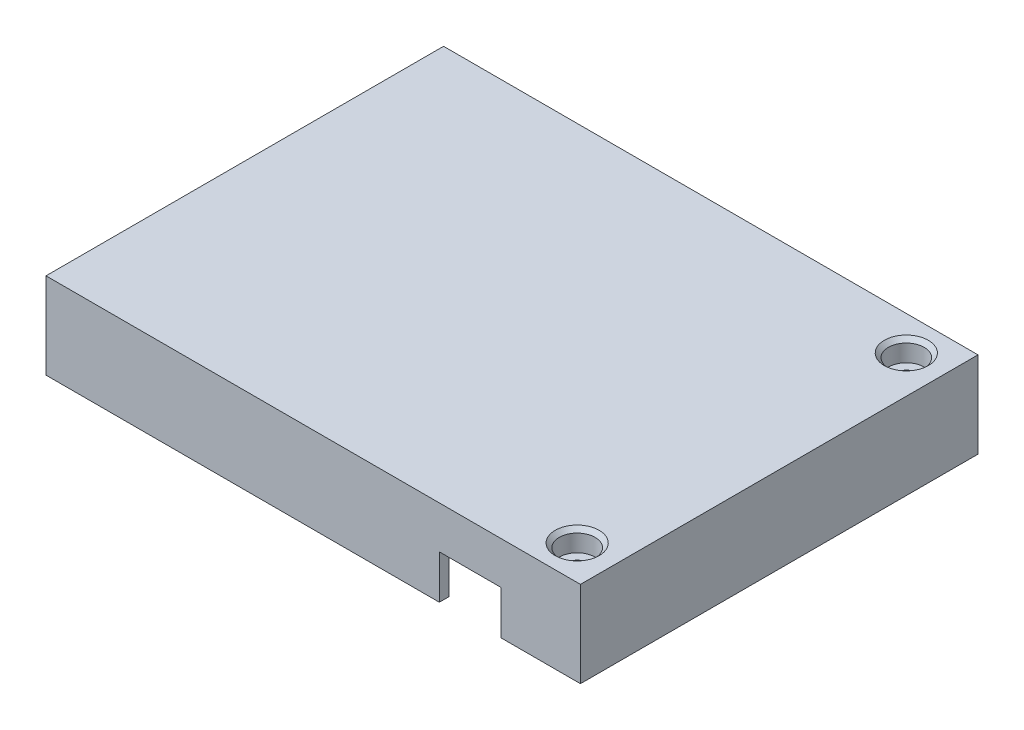
SolidWorks part; units mm, degrees
ref_plane "Front Plane" through (0, 0, 0) normal (0, 0, 1) x (1, 0, 0)
ref_plane "Top Plane" through (0, 0, 0) normal (0, 1, 0) x (1, 0, 0)
ref_plane "Right Plane" through (0, 0, 0) normal (1, 0, 0) x (0, 0, -1)
sketch "Sketch1" plane through (0, 0, 0) normal (0, 1, 0) x (1, 0, 0)
  line L1 (-41, -30.5) -> (41, -30.5)
  line L2 (-41, -30.5) -> (-41, 30.5)
  line L3 (-41, 30.5) -> (41, 30.5)
  line L4 (41, -30.5) -> (41, 30.5)
  line L5 (-41, -30.5) -> (41, 30.5) construction
  line L6 (-41, 30.5) -> (41, -30.5) construction
  point P0 (0, 0)
  dimension "D1" = 61
  dimension "D2" = 82
extrude "Boss-Extrude1" add sketch "Sketch1" along normal blind 13.2
shell "Shell2" thickness 1.5
sketch "Sketch2" plane through (0, 11.7, 0) normal (0, -1, 0) x (1, 0, 0)
  line L0 (-41, 30.5) -> (41, 30.5) construction
  line L1 (39.5, 29) -> (31.75, 29)
  line L2 (39.5, 29) -> (39.5, 21.25)
  line L3 (39.5, 21.25) -> (31.75, 21.25)
  line L4 (31.75, 29) -> (31.75, 21.25)
  dimension "D1" = 9.25
extrude "Boss-Extrude2" add sketch "Sketch2" along normal offset from surface (10 mm away) 1.7 up to face at (0, 0, 0)
mirror "Mirror1" about plane through (0, 0, 0) normal (1, 0, 0) of "Boss-Extrude2"
sketch "Sketch3" plane through (0, 13.2, 0) normal (0, 1, 0) x (1, 0, 0)
  line L0 (41, -30.5) -> (41, 30.5) construction
  line L1 (35.25, -25.25) -> (35.25, -30.5) construction
  line L2 (-41, -30.5) -> (41, -30.5) construction
  line L3 (35.25, -25.25) -> (41, -25.25) construction
  point P1 (35.25, -25.25)
  dimension "D1" = 5.75
  dimension "D2" = 5.25
sketch "Sketch7" plane through (0, 13.2, 0) normal (0, 1, 0) x (1, 0, 0)
  point P0 (35.25, -25.25)
hole_wizard "CBORE for M5 Hex Head Bolt1" positions "Sketch7" profile "Sketch6" counterbore size "M5" standard "ANSI Metric" end condition through all
sketch "Sketch6" plane through (35.25, 13.2, 25.25) normal (1, 0, 0) x (0, 0, 1)
  line L0 (0, 0) -> (0, 13.2)
  line L1 (0, 13.2) -> (1.375, 13.2)
  line L3 (1.375, 13.2) -> (1.375, 3.25)
  line L4 (2.75, 3.25) -> (1.375, 3.25)
  line L5 (2.75, 3.25) -> (2.75, 0.625)
  line L6 (2.75, 0.625) -> (3.375, 0)
  line L7 (3.375, 0) -> (0, 0)
  line L8 (-2.75, 0.625) -> (-3.375, 0) construction
  line L11 (0, -6.35) -> (0, 107.95) construction
  dimension "Thru Hole Dia." = 2.75
  dimension "Thru Hole Depth" = 13.2
  dimension "C'Bore Dia." = 5.5
  dimension "C'Bore Depth" = 3.25
  dimension "Near C'Sink Dia." = 6.75
  dimension "Near C'Sink Angle" = 90
sketch "Sketch8" plane through (0, 1.7, 0) normal (0, -1, 0) x (1, 0, 0)
  line L0 (-39.5, 29) -> (-31.75, 29) construction
  line L2 (-41, -30.5) -> (-41, 30.5) construction
  line L3 (-36.35, 29) -> (-33.15, 29)
  arc A0 (-36.35, 29) -> (-33.15, 29) centre (-34.75, 29) ccw
  circle A1 centre (-34.75, 29) radius 1.75 construction
  dimension "D1" = 3.2
  dimension "D3" = 3.5
  dimension "D2" = 8
extrude "Boss-Extrude3" add sketch "Sketch8" along normal up to surface (1.7 mm away) up to face at (0, 0, 0)
mirror "Mirror2" about plane through (0, 0, 0) normal (0, 0, 1) of "Boss-Extrude3", "CBORE for M5 Hex Head Bolt1", "Boss-Extrude2", "Mirror1"
sketch "Sketch9" plane through (0, 0, 30.5) normal (0, 0, 1) x (1, 0, 0)
  line L0 (-41, 0) -> (41, 0) construction
  line L1 (19.35, 0) -> (28.85, 0)
  line L2 (19.35, 0) -> (19.35, 6.7)
  line L3 (19.35, 6.7) -> (28.85, 6.7)
  line L4 (28.85, 0) -> (28.85, 6.7)
  line L5 (41, 13.2) -> (41, 0) construction
  line L7 (-31.75, 11.7) -> (31.75, 11.7) construction
  dimension "D1" = 9.5
  dimension "D2" = 12.15
  dimension "D3" = 5
extrude "Cut-Extrude1" cut sketch "Sketch9" against normal up to next and the other way through all
